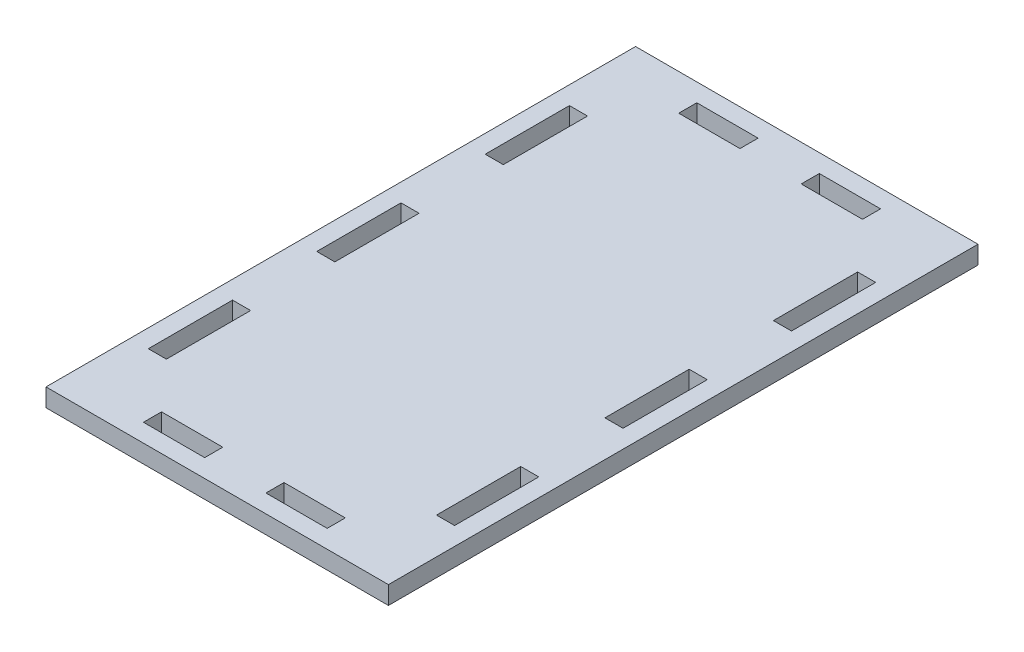
SolidWorks part; units mm, degrees
ref_plane "Front Plane" through (0, 0, 0) normal (0, 0, 1) x (1, 0, 0)
ref_plane "Top Plane" through (0, 0, 0) normal (0, 1, 0) x (1, 0, 0)
ref_plane "Right Plane" through (0, 0, 0) normal (1, 0, 0) x (0, 0, -1)
sketch "Sketch1" plane through (0, 0, 0) normal (0, 1, 0) x (1, 0, 0)
  line L1 (0, 0) -> (56.8, 0)
  line L2 (0, 0) -> (0, 97.79)
  line L3 (0, 97.79) -> (56.8, 97.79)
  line L4 (56.8, 0) -> (56.8, 97.79)
  dimension "D1" = 56.8
  dimension "D2" = 97.79
extrude "Boss-Extrude1" add sketch "Sketch1" along normal blind 3
sketch "Sketch2" plane through (0, 3, 0) normal (0, 1, 0) x (1, 0, 0)
  line L0 (56.8, 97.79) -> (0, 97.79) construction
  line L1 (13.16, 94.79) -> (23.32, 94.79)
  line L2 (13.16, 94.79) -> (13.16, 91.79)
  line L3 (13.16, 91.79) -> (23.32, 91.79)
  line L4 (23.32, 94.79) -> (23.32, 91.79)
  line L5 (33.48, 94.79) -> (43.64, 94.79)
  line L6 (33.48, 94.79) -> (33.48, 91.79)
  line L7 (33.48, 91.79) -> (43.64, 91.79)
  line L8 (43.64, 94.79) -> (43.64, 91.79)
  line L9 (50.8, 83.82) -> (53.8, 83.82)
  line L10 (50.8, 83.82) -> (50.8, 69.85)
  line L11 (50.8, 69.85) -> (53.8, 69.85)
  line L12 (53.8, 83.82) -> (53.8, 69.85)
  line L13 (50.8, 55.88) -> (53.8, 55.88)
  line L14 (50.8, 55.88) -> (50.8, 41.91)
  line L15 (50.8, 41.91) -> (53.8, 41.91)
  line L16 (53.8, 55.88) -> (53.8, 41.91)
  line L17 (50.8, 27.94) -> (53.8, 27.94)
  line L18 (50.8, 27.94) -> (50.8, 13.97)
  line L19 (50.8, 13.97) -> (53.8, 13.97)
  line L20 (53.8, 27.94) -> (53.8, 13.97)
  line L21 (56.8, 0) -> (56.8, 97.79) construction
  line L22 (52.3, 83.82) -> (52.3, 97.79) construction
  line L23 (52.3, 69.85) -> (52.3, 55.88) construction
  line L24 (52.3, 41.91) -> (52.3, 27.94) construction
  line L25 (52.3, 13.97) -> (52.3, 0) construction
  line L26 (0, 0) -> (56.8, 0) construction
  line L27 (43.64, 93.29) -> (53.8, 93.29) construction
  line L28 (33.48, 93.29) -> (23.32, 93.29) construction
  line L29 (13.16, 93.29) -> (3, 93.29) construction
  line L30 (0, 97.79) -> (0, 0) construction
  line L31 (28.4, 97.79) -> (28.4, 0) construction
  line L32 (0, 48.895) -> (56.8, 48.895) construction
  line L33 (43.64, 3) -> (43.64, 6)
  line L34 (33.48, 6) -> (43.64, 6)
  line L35 (33.48, 3) -> (43.64, 3)
  line L36 (33.48, 3) -> (33.48, 6)
  line L37 (23.32, 3) -> (23.32, 6)
  line L38 (13.16, 3) -> (23.32, 3)
  line L39 (13.16, 6) -> (23.32, 6)
  line L40 (13.16, 3) -> (13.16, 6)
  line L41 (6, 83.82) -> (3, 83.82)
  line L42 (3, 83.82) -> (3, 69.85)
  line L43 (6, 83.82) -> (6, 69.85)
  line L44 (6, 69.85) -> (3, 69.85)
  line L45 (6, 41.91) -> (3, 41.91)
  line L46 (6, 55.88) -> (3, 55.88)
  line L47 (6, 55.88) -> (6, 41.91)
  line L48 (3, 55.88) -> (3, 41.91)
  line L49 (6, 27.94) -> (3, 27.94)
  line L50 (6, 13.97) -> (3, 13.97)
  line L51 (3, 27.94) -> (3, 13.97)
  line L52 (6, 27.94) -> (6, 13.97)
  line L53 (53.8, 83.82) -> (53.8, 97.79) construction
  line L54 (3, 83.82) -> (3, 97.79) construction
  point P34 (52.3, 55.88)
  point P35 (52.3, 27.94)
  point P44 (23.32, 93.29)
  dimension "D1" = 3
  dimension "D2" = 3
  dimension "D3" = 3
  dimension "D4" = 3
  dimension "D5" = 3
  dimension "D6" = 3
  dimension "D7" = 3
  dimension "D8" = 3
  dimension "D9" = 3
  dimension "D10" = 13.97
  dimension "D11" = 3
  dimension "D12" = 10.16
extrude "Cut-Extrude1" cut sketch "Sketch2" against normal through all
sketch "Sketch3" [suppressed] plane through (0, 3, 0) normal (0, 1, 0) x (1, 0, 0)
  line L0 (28.4, 97.79) -> (28.4, 0) construction
  line L1 (6, 69.85) -> (6, 83.82) construction
  line L2 (0, 0) -> (56.8, 0) construction
  line L3 (16.16, 48.895) -> (28.4, 48.895) construction
  line L4 (11.08, 77.47) -> (16.16, 77.47)
  line L5 (11.08, 77.47) -> (11.08, 20.32)
  line L6 (11.08, 20.32) -> (16.16, 20.32)
  line L7 (16.16, 77.47) -> (16.16, 20.32)
  line L8 (56.8, 97.79) -> (0, 97.79) construction
  point P11 (28.4, 97.79)
  dimension "D1" = 57.15
  dimension "D2" = 5.08
  dimension "D4" = 5.08
extrude "Cut-Extrude2" [suppressed] cut sketch "Sketch3" against normal through all
